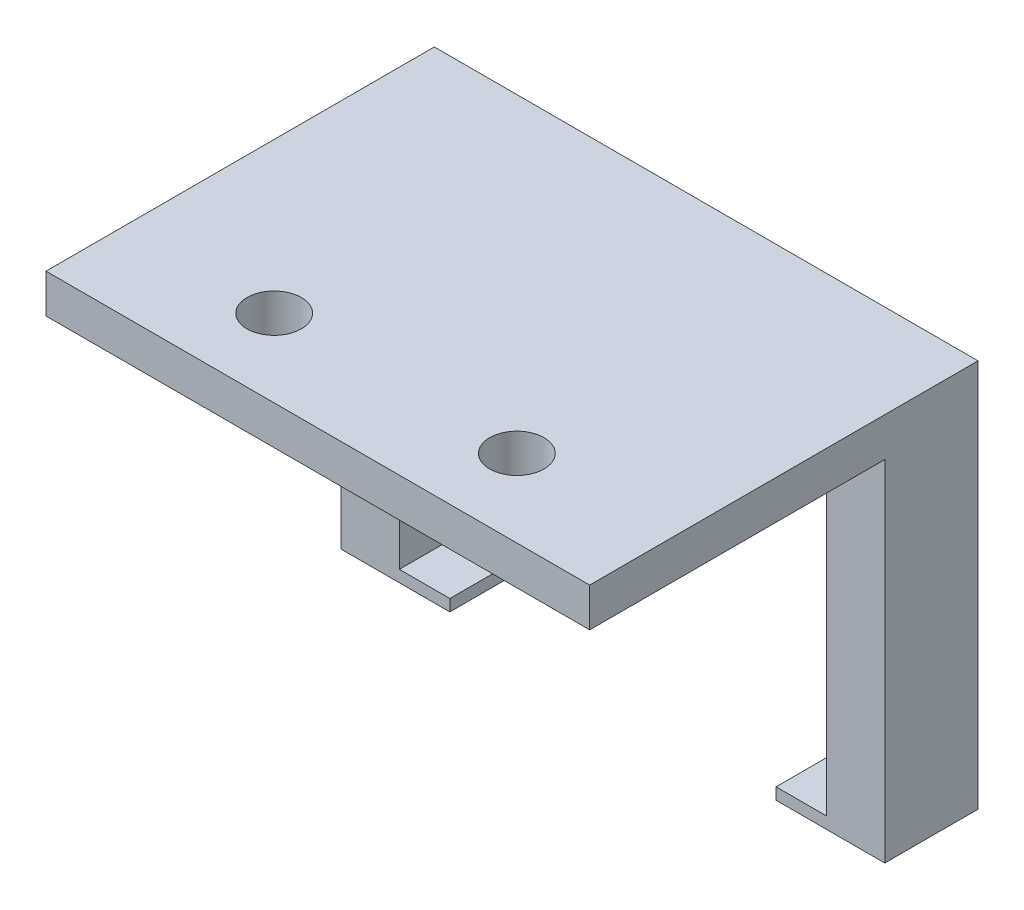
SolidWorks part; units mm, degrees
material "Custom Plastic"
ref_plane "Front Plane" through (0, 0, 0) normal (0, 0, 1) x (1, 0, 0)
ref_plane "Top Plane" through (0, 0, 0) normal (0, 1, 0) x (1, 0, 0)
ref_plane "Right Plane" through (0, 0, 0) normal (1, 0, 0) x (0, 0, -1)
sketch "Sketch3" plane through (0, 0, 0) normal (0, 1, 0) x (1, 0, 0)
  line L1 (-11.5173, 12.4673) -> (24.0427, 12.4673)
  line L2 (-11.5173, 12.4673) -> (-11.5173, -12.9327)
  line L3 (-11.5173, -12.9327) -> (24.0427, -12.9327)
  line L4 (24.0427, 12.4673) -> (24.0427, -12.9327)
  circle A0 centre (-1.6748, -7.8527) radius 1.778
  circle A2 centre (14.2002, -7.8527) radius 1.778
  dimension "D2" = 3.556
  dimension "D3" = 3.556
  dimension "D1" = 25.4
  dimension "1" = 35.56
  dimension "D4" = 15.875
  dimension "D5" = 9.8425
  dimension "D6" = 20.32
extrude "Boss-Extrude3" add sketch "Sketch3" along normal blind 2.54
sketch "Sketch4" plane through (0, 0, 0) normal (0, -1, 0) x (1, 0, 0)
  line L0 (-11.5173, -12.4673) -> (-11.5173, 12.9327) construction
  line L1 (-11.5173, -1.2913) -> (-7.7073, -1.2913)
  line L2 (-11.5173, -1.2913) -> (-11.5173, -12.4673)
  line L3 (-11.5173, -12.4673) -> (-7.7073, -12.4673)
  line L4 (-7.7073, -1.2913) -> (-7.7073, -12.4673)
  line L5 (24.0427, -12.4673) -> (-11.5173, -12.4673) construction
  line L6 (-11.5173, 12.9327) -> (24.0427, 12.9327) construction
  line L7 (24.0427, 12.9327) -> (24.0427, -12.4673) construction
  line L8 (24.0427, -1.2913) -> (20.2327, -1.2913)
  line L9 (24.0427, -1.2913) -> (24.0427, -12.4673)
  line L10 (24.0427, -12.4673) -> (20.2327, -12.4673)
  line L11 (20.2327, -1.2913) -> (20.2327, -12.4673)
  dimension "D1" = 14.224
  dimension "D2" = 3.81
  dimension "D3" = 14.224
  dimension "D4" = 3.81
extrude "Boss-Extrude4" add sketch "Sketch4" along normal blind 22.86
sketch "Sketch5" plane through (-7.7073, 0, 0) normal (1, 0, 0) x (0, 0, -1)
  line L0 (1.2913, -22.86) -> (1.2913, 0) construction
  line L1 (1.2913, -22.098) -> (12.4673, -22.098)
  line L2 (1.2913, -22.098) -> (1.2913, -22.86)
  line L3 (1.2913, -22.86) -> (12.4673, -22.86)
  line L4 (12.4673, -22.098) -> (12.4673, -22.86)
  dimension "D1" = 0.762
extrude "Boss-Extrude5" add sketch "Sketch5" along normal blind 3.302
sketch "Sketch6" plane through (20.2327, 0, 0) normal (-1, 0, 0) x (0, 0, 1)
  line L0 (-12.4673, 2.54) -> (-12.4673, -22.86) construction
  line L1 (-12.4673, -22.098) -> (-1.2913, -22.098)
  line L2 (-12.4673, -22.098) -> (-12.4673, -22.86)
  line L3 (-12.4673, -22.86) -> (-1.2913, -22.86)
  line L4 (-1.2913, -22.098) -> (-1.2913, -22.86)
  dimension "D1" = 0.762
extrude "Boss-Extrude6" add sketch "Sketch6" along normal blind 3.302
sketch "Sketch7" plane through (0, 0, -1.2913) normal (0, 0, 1) x (1, 0, 0)
  line L1 (-11.5173, 0) -> (24.0427, 0)
  line L2 (-11.5173, 0) -> (-11.5173, -22.86)
  line L3 (-11.5173, -22.86) -> (24.0427, -22.86)
  line L4 (24.0427, 0) -> (24.0427, -22.86)
extrude "Cut-Extrude1" cut sketch "Sketch7" against normal blind 5.08
